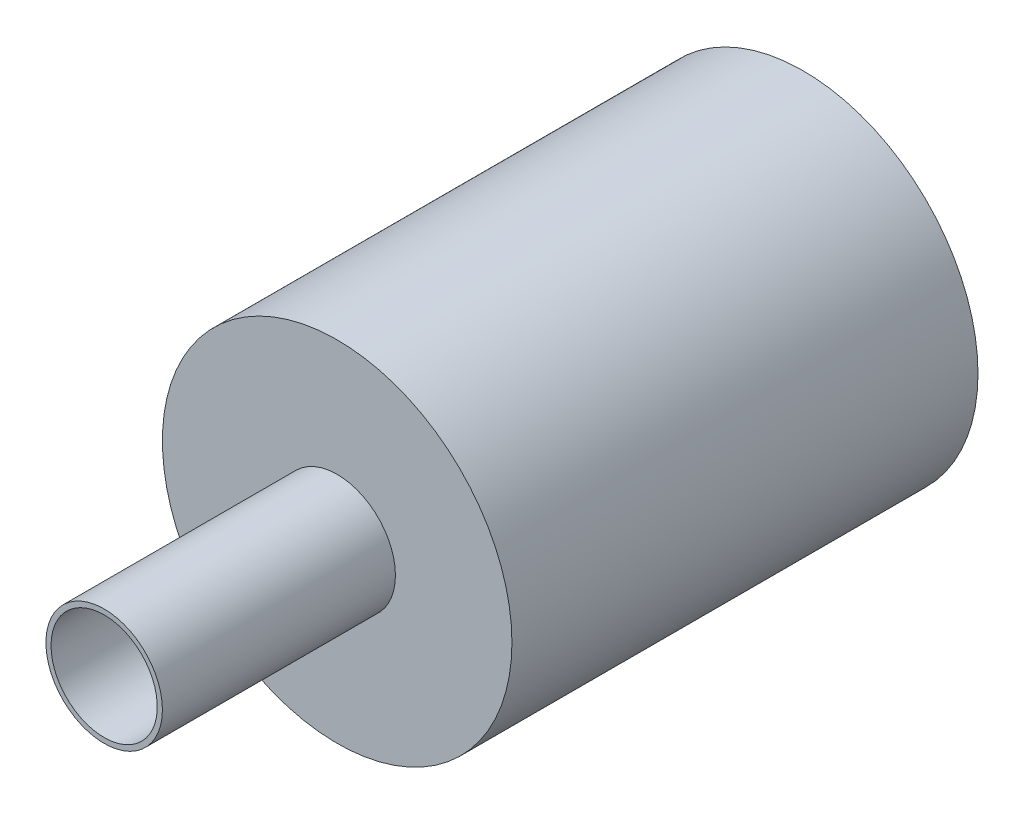
SolidWorks part; units mm, degrees
ref_plane "Front Plane" through (0, 0, 0) normal (0, 0, 1) x (1, 0, 0)
ref_plane "Top Plane" through (0, 0, 0) normal (0, 1, 0) x (1, 0, 0)
ref_plane "Right Plane" through (0, 0, 0) normal (1, 0, 0) x (0, 0, -1)
sketch "Sketch1" plane through (0, 0, 0) normal (0, 0, 1) x (1, 0, 0)
  circle A0 centre (0, 0) radius 9.525
  dimension "D1" = 19.05
extrude "Boss-Extrude1" add sketch "Sketch1" along normal blind 25.4
sketch "Sketch2" plane through (0, 0, 25.4) normal (0, 0, 1) x (1, 0, 0)
  circle A0 centre (0, 0) radius 3.175
  dimension "D1" = 6.35
extrude "Boss-Extrude2" add sketch "Sketch2" along normal blind 12.7
hole_wizard "#1 (0.228) Diameter Hole1" positions "Sketch3" profile "Sketch4" hole size "#1" standard "ANSI Inch" end condition through all
sketch "Sketch3" plane through (0, 0, 0) normal (0, 0, -1) x (-1, 0, 0)
  point P0 (0, 0)
sketch "Sketch4" plane through (0, 0, 0) normal (1, 0, 0) x (0, 1, 0)
  line L0 (0, 0) -> (0, 38.1)
  line L1 (0, 38.1) -> (2.8956, 38.1)
  line L2 (2.8956, 38.1) -> (2.8956, 0)
  line L5 (2.8956, 0) -> (0, 0)
  line L11 (0, -6.35) -> (0, 107.95) construction
  dimension "Thru Hole Dia." = 5.7912
  dimension "Thru Hole Depth" = 38.1
hole_wizard "35/64 (0.54688) Diameter Hole1" positions "Sketch5" profile "Sketch6" hole size "35/64" standard "ANSI Inch"
sketch "Sketch5" plane through (0, 0, 0) normal (0, 0, -1) x (-1, 0, 0)
  point P0 (0, 0)
sketch "Sketch6" plane through (0, 0, 0) normal (1, 0, 0) x (0, 1, 0)
  line L0 (0, 0) -> (0, 22.9692)
  line L1 (0, 22.9692) -> (6.9454, 18.796)
  line L2 (6.9454, 18.796) -> (6.9454, 0)
  line L5 (6.9454, 0) -> (0, 0)
  line L10 (0, 22.9692) -> (-6.9454, 18.796) construction
  line L11 (0, -6.35) -> (0, 107.95) construction
  dimension "Hole Dia." = 13.8908
  dimension "Hole Depth" = 18.796
  dimension "Drill Angle" = 118
